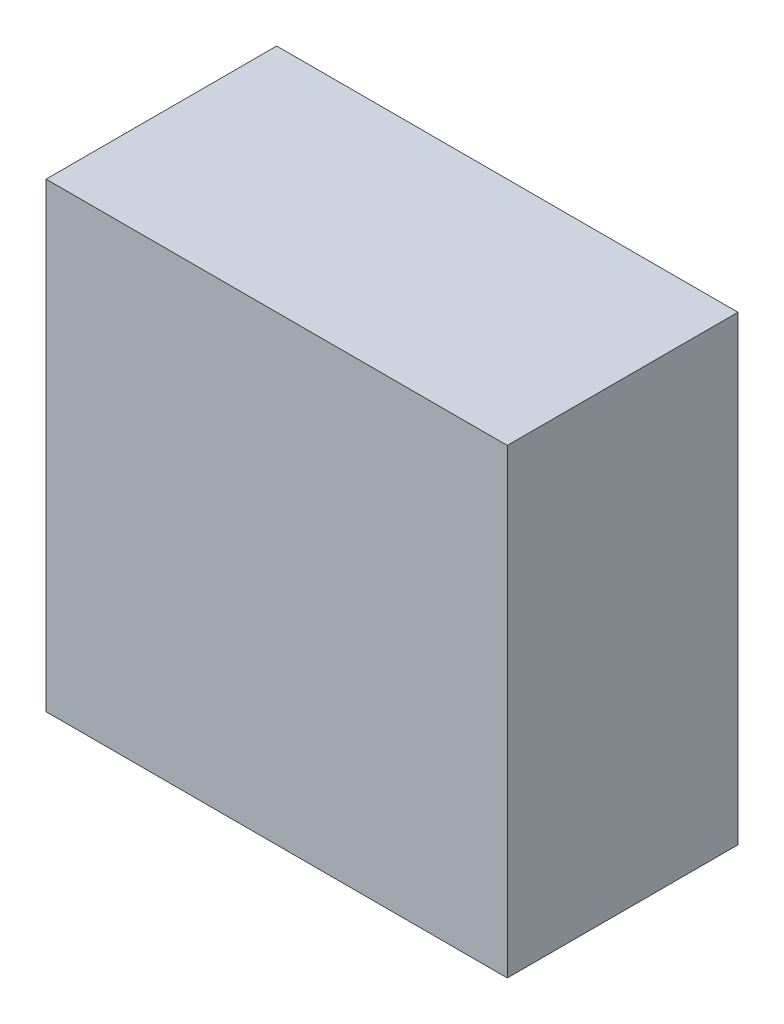
SolidWorks part; units mm, degrees
material "ASTM A36 Steel"
ref_plane "Front Plane" through (0, 0, 0) normal (0, 0, 1) x (1, 0, 0)
ref_plane "Top Plane" through (0, 0, 0) normal (0, 1, 0) x (1, 0, 0)
ref_plane "Right Plane" through (0, 0, 0) normal (1, 0, 0) x (0, 0, -1)
sketch "Sketch1" plane through (0, 0, 0) normal (0, 0, 1) x (1, 0, 0)
  line L1 (63.5, 63.5) -> (-63.5, 63.5)
  line L2 (63.5, 63.5) -> (63.5, -63.5)
  line L3 (63.5, -63.5) -> (-63.5, -63.5)
  line L4 (-63.5, 63.5) -> (-63.5, -63.5)
  line L5 (63.5, 63.5) -> (-63.5, -63.5) construction
  line L6 (63.5, -63.5) -> (-63.5, 63.5) construction
  point P0 (0, 0)
  dimension "D1" = 127
  dimension "D2" = 127
extrude "Boss-Extrude1" add sketch "Sketch1" along normal blind 63.5
sketch "Sketch2" plane through (0, 0, 0) normal (0, 0, -1) x (-1, 0, 0)
  circle A0 centre (0, 0) radius 12.7
  dimension "D1" = 25.4
extrude "Boss-Extrude2" add sketch "Sketch2" along normal blind 50.8
